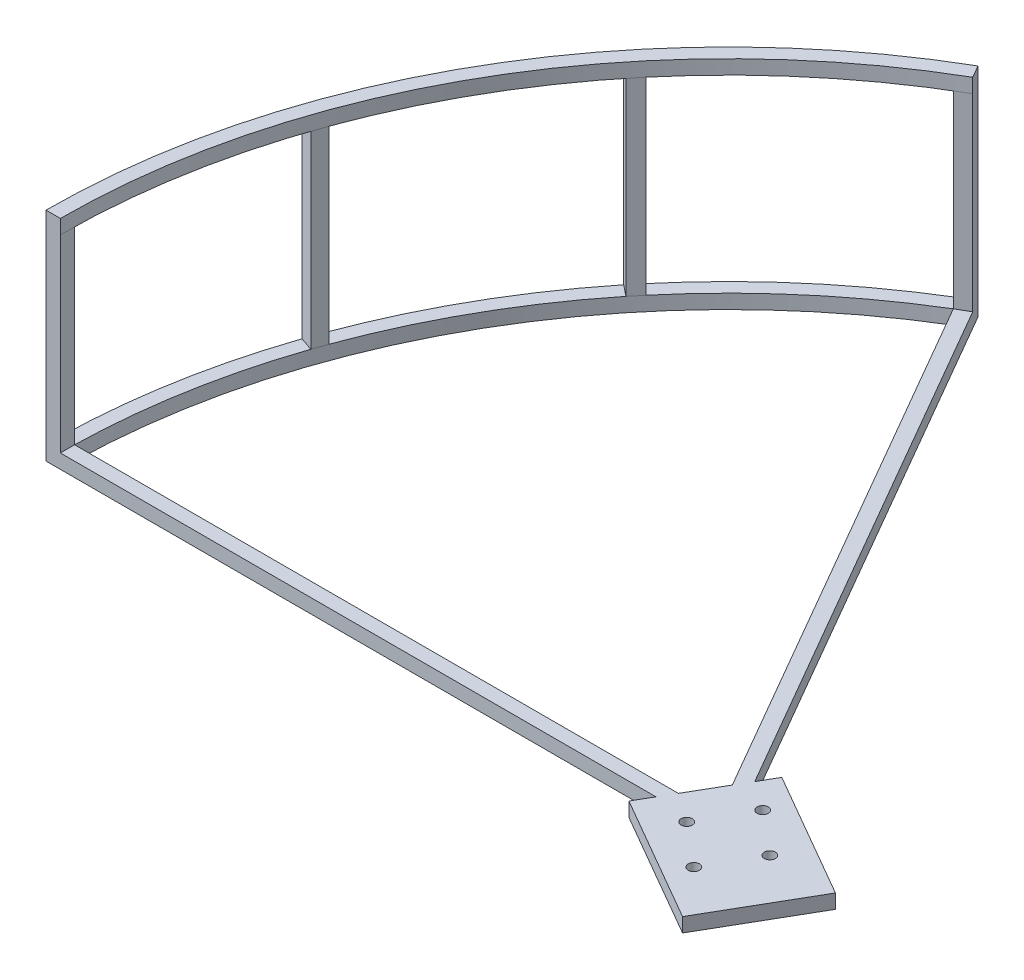
SolidWorks part; units mm, degrees
material "ABS"
ref_plane "Front Plane" through (0, 0, 0) normal (0, 0, 1) x (1, 0, 0)
ref_plane "Top Plane" through (0, 0, 0) normal (0, 1, 0) x (1, 0, 0)
ref_plane "Right Plane" through (0, 0, 0) normal (1, 0, 0) x (0, 0, -1)
sketch "Sketch1" plane through (0, 90.0552, 0) normal (0, 1, 0) x (1, 0, 0)
  line L4 (-138.7289, 21.9144) -> (-167.0739, 38.2794)
  line L5 (-167.0739, 38.2794) -> (-179.5739, 16.6287)
  line L6 (-179.5739, 16.6287) -> (-151.2289, 0.2637)
  line L7 (-151.2289, 0.2637) -> (-138.7289, 21.9144)
  line L8 (-138.7289, 21.9144) -> (-167.0739, 38.2794)
  line L9 (-167.0739, 38.2794) -> (-179.5739, 16.6287)
  line L10 (-179.5739, 16.6287) -> (-151.2289, 0.2637)
  line L11 (-151.2289, 0.2637) -> (-138.7289, 21.9144)
  circle A0 centre (-169.0897, 19.0591) radius 1.25 construction
  circle A1 centre (-162.8798, 29.8149) radius 1.25 construction
  circle A2 centre (-153.3377, 21.8652) radius 1.25 construction
  circle A3 centre (-159.5475, 11.1094) radius 1.25 construction
  circle A4 centre (-169.0897, 19.0591) radius 1.25
  circle A5 centre (-162.8798, 29.8149) radius 1.25
  circle A6 centre (-153.3377, 21.8652) radius 1.25
  circle A7 centre (-159.5475, 11.1094) radius 1.25
  dimension "D1" = 0
extrude "Boss-Extrude1" add sketch "Sketch1" along normal blind 3.175
sketch "Sketch2" plane through (0, 93.2302, 0) normal (0, 1, 0) x (1, 0, 0)
  line L0 (-161.2137, 20.4622) -> (-237.4137, 152.4444)
  line L1 (-161.2137, 20.4622) -> (-313.6137, 20.4622)
  line L2 (-173.3239, 27.454) -> (-149.1034, 13.4703) construction
  line L3 (-166.7129, 23.6372) -> (-238.5589, 148.078)
  line L4 (-166.7129, 23.6372) -> (-310.4049, 23.6372)
  arc A0 (-237.4137, 152.4444) -> (-313.6137, 20.4622) centre (-161.2137, 20.4622) ccw
  arc A1 (-238.5589, 148.078) -> (-310.4049, 23.6372) centre (-161.2137, 20.4622) ccw
  dimension "D1" = 60
  dimension "D2" = 30
  dimension "D3" = 152.4
  dimension "D4" = 3.175
extrude "Boss-Extrude2" add sketch "Sketch2" against normal blind 3.175
sketch "Sketch3" plane through (0, 93.2302, 0) normal (0, 1, 0) x (1, 0, 0)
  line L0 (-238.5589, 148.078) -> (-240.2045, 150.7933)
  line L1 (-238.5589, 148.078) -> (-235.8093, 149.6655)
  line L2 (-169.2872, 34.4459) -> (-237.4137, 152.4444) construction
  line L3 (-235.8093, 149.6655) -> (-237.4137, 152.4444)
  line L4 (-161.2137, 20.4622) -> (-293.1959, 96.6622) construction
  line L5 (-310.4049, 20.4622) -> (-313.6137, 20.4622)
  line L6 (-310.4049, 23.6372) -> (-310.4049, 20.4622)
  line L7 (-310.4049, 23.6372) -> (-313.5792, 23.7047)
  line L8 (-277.5416, 113.9282) -> (-280.0167, 115.9169)
  line L9 (-275.5008, 116.3604) -> (-277.9588, 118.423)
  line L10 (-277.5416, 113.9282) -> (-275.5008, 116.3604)
  line L11 (-302.4935, 68.505) -> (-305.4994, 69.5272)
  line L12 (-301.4075, 71.4886) -> (-304.4228, 72.586)
  line L13 (-302.4935, 68.505) -> (-301.4075, 71.4886)
  line L17 (-310.4049, 17.2872) -> (-310.4049, 20.4622) [skipped]
  line L18 (-310.4049, 17.2872) -> (-313.5792, 17.2196) [skipped]
  line L19 (-310.4049, 20.4622) -> (-313.6137, 20.4622) [skipped]
  arc A0 (-237.4137, 152.4444) -> (-313.6137, 20.4622) centre (-161.2137, 20.4622) ccw construction
  arc A1 (-237.4137, 152.4444) -> (-240.2045, 150.7933) centre (-161.2137, 20.4622) ccw
  arc A2 (-313.6137, 20.4622) -> (-313.5792, 23.7047) centre (-161.2137, 20.4622) cw
  arc A3 (-277.9588, 118.423) -> (-280.0167, 115.9169) centre (-161.2137, 20.4622) ccw
  arc A4 (-304.4228, 72.586) -> (-305.4994, 69.5272) centre (-161.2137, 20.4622) ccw
  arc A6 (-313.6137, 20.4622) -> (-313.5792, 17.2196) centre (-161.2137, 20.4622) ccw [skipped]
  point P28 (-161.2137, 20.4622)
  dimension "D1" = 4
extrude "Boss-Extrude3" add sketch "Sketch3" along normal blind 42.2
sketch "Sketch4" plane through (0, 135.4302, 0) normal (0, 1, 0) x (1, 0, 0)
  line L0 (-173.3239, 27.454) -> (-149.1034, 13.4703) construction
  line L1 (-235.8093, 149.6655) -> (-237.4137, 152.4444) construction
  line L2 (-169.2872, 34.4459) -> (-235.8093, 149.6655) construction
  line L3 (-237.4137, 152.4444) -> (-235.8093, 149.6655)
  line L4 (-313.6137, 20.4622) -> (-310.4049, 20.4622)
  arc A0 (-313.6137, 20.4622) -> (-237.4137, 152.4444) centre (-161.2137, 20.4622) cw
  arc A1 (-310.4049, 20.4622) -> (-235.8093, 149.6655) centre (-161.2137, 20.4622) cw
extrude "Boss-Extrude4" add sketch "Sketch4" along normal blind 3.175
